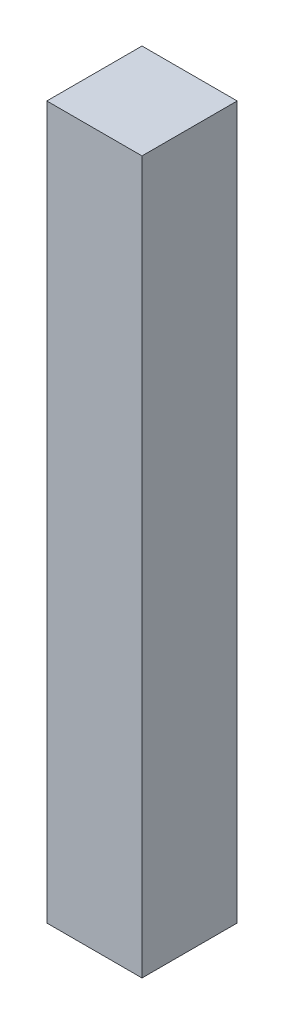
SolidWorks part; units mm, degrees
ref_plane "Front Plane" through (0, 0, 0) normal (0, 0, 1) x (1, 0, 0)
ref_plane "Top Plane" through (0, 0, 0) normal (0, 1, 0) x (1, 0, 0)
ref_plane "Right Plane" through (0, 0, 0) normal (1, 0, 0) x (0, 0, -1)
sketch "Sketch1" plane through (0, 0, 0) normal (0, 1, 0) x (1, 0, 0)
  line L1 (-12.7, -12.7) -> (12.7, -12.7)
  line L2 (-12.7, -12.7) -> (-12.7, 12.7)
  line L3 (-12.7, 12.7) -> (12.7, 12.7)
  line L4 (12.7, -12.7) -> (12.7, 12.7)
  line L5 (-12.7, -12.7) -> (12.7, 12.7) construction
  line L6 (-12.7, 12.7) -> (12.7, -12.7) construction
  point P0 (0, 0)
  dimension "D1" = 25.4
extrude "Boss-Extrude1" add sketch "Sketch1" along normal blind 190
